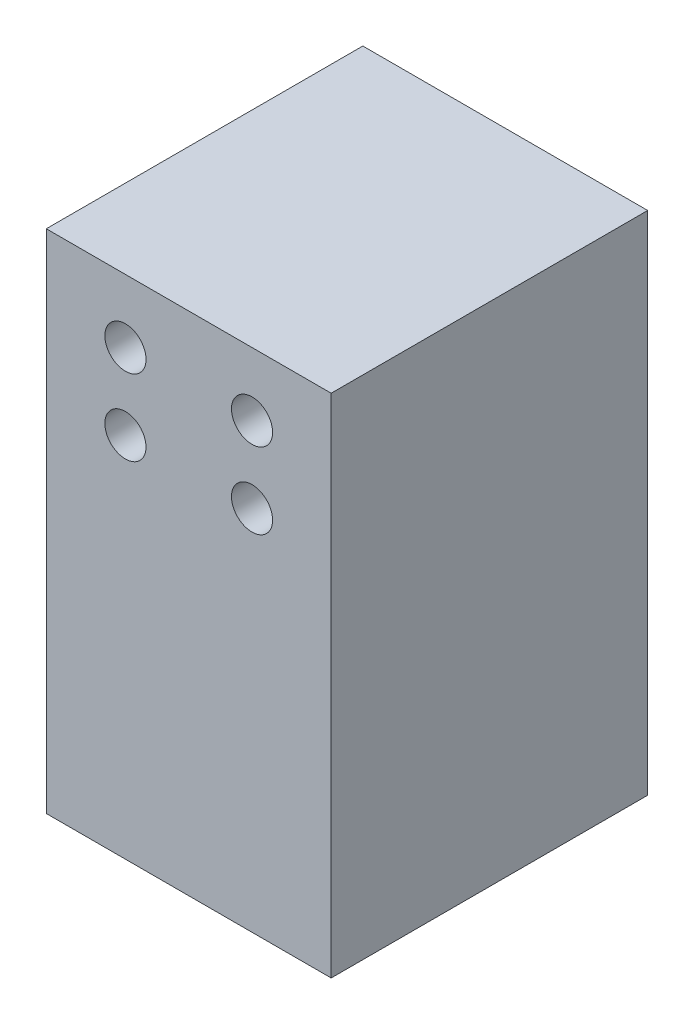
SolidWorks part; units mm, degrees
ref_plane "Front Plane" through (0, 0, 0) normal (0, 0, 1) x (1, 0, 0)
ref_plane "Top Plane" through (0, 0, 0) normal (0, 1, 0) x (1, 0, 0)
ref_plane "Right Plane" through (0, 0, 0) normal (1, 0, 0) x (0, 0, -1)
sketch "Sketch1" plane through (0, 0, 0) normal (0, 0, 1) x (1, 0, 0)
  line L1 (-22.5, -40) -> (22.5, -40)
  line L2 (-22.5, -40) -> (-22.5, 40)
  line L3 (-22.5, 40) -> (22.5, 40)
  line L4 (22.5, -40) -> (22.5, 40)
  line L5 (0, 40) -> (0, -40) construction
  line L6 (-22.5, 0) -> (22.5, 0) construction
  point P0 (0, 0)
  dimension "D1" = 80
  dimension "D2" = 45
extrude "Boss-Extrude1" add sketch "Sketch1" along normal mid plane 50
sketch "Sketch3" plane through (0, 0, 0) normal (0, 0, 1) x (1, 0, 0)
  line L0 (0, 40) -> (0, 0) construction
  line L1 (22.5, 40) -> (-22.5, 40) construction
  line L2 (-10, 30) -> (10, 30)
  line L3 (-22.5, 40) -> (-22.5, -40) construction
  circle A0 centre (-10, 30) radius 3.25
  circle A1 centre (10, 30) radius 3.25
  point P8 (0, 30)
  dimension "D1" = 6.5
  dimension "D2" = 12.5
  dimension "D3" = 10
extrude "Cut-Extrude1" cut sketch "Sketch3" against normal through all both and the other way through all contours A0 | A1
pattern_linear "LPattern1" count 2 spacing 12 along (0, -1, 0) of "Cut-Extrude1"
sketch "Sketch4" plane through (0, -40, 0) normal (0, -1, 0) x (1, 0, 0)
  line L1 (-12, -17.5) -> (12, -17.5)
  line L2 (-12, -17.5) -> (-12, 17.5)
  line L3 (-12, 17.5) -> (12, 17.5)
  line L4 (12, -17.5) -> (12, 17.5)
  line L5 (0, 17.5) -> (0, -17.5) construction
  line L6 (-12, 0) -> (12, 0) construction
  circle A0 centre (-12, 17.5) radius 2.25
  circle A1 centre (12, 17.5) radius 2.25
  circle A2 centre (-12, -17.5) radius 2.25
  circle A3 centre (12, -17.5) radius 2.25
  point P0 (0, 0)
  dimension "D1" = 4.5
  dimension "D2" = 24
  dimension "D3" = 35
extrude "Cut-Extrude2" cut sketch "Sketch4" against normal blind 15 contours A0 | A1 | A3 | A2
